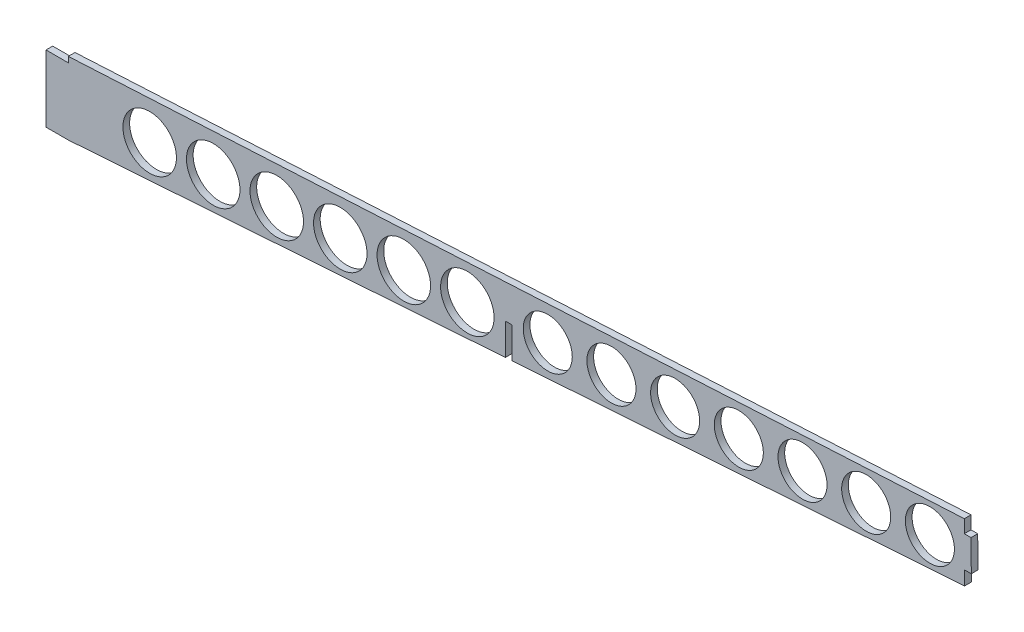
SolidWorks part; units mm, degrees
material "Pine"
ref_plane "Front Plane" through (0, 0, 0) normal (0, 0, 1) x (1, 0, 0)
ref_plane "Top Plane" through (0, 0, 0) normal (0, 1, 0) x (1, 0, 0)
ref_plane "Right Plane" through (0, 0, 0) normal (1, 0, 0) x (0, 0, -1)
sketch "Sketch1" plane through (0, 0, 0) normal (0, 0, 1) x (1, 0, 0)
  line L0 (-415, 15) -> (-405, 15) construction
  line L4 (-415, 0) -> (-415, 30)
  line L6 (-415, 30) -> (-405, 30)
  line L7 (-415, 0) -> (-405, 0)
  line L8 (-415, 0) -> (0, 0) construction
  line L9 (-415, 15) -> (0, 44.0196) construction
  line L10 (-0.2558, 54.0196) -> (0, 28.0209)
  line L11 (0, 44.0196) -> (0, 0) construction
  line L13 (-405, 0) -> (0, 28.0209)
  line L14 (-405, 30) -> (-405, 32.5)
  line L15 (-405, 32.5) -> (-0.2558, 54.0196)
  dimension "D1" = 30
  dimension "D2" = 10
  dimension "D3" = 415
  dimension "D4" = 4
  dimension "D5" = 26
  dimension "D6" = 10
  dimension "D7" = 93.394
  dimension "D8" = 2.5
extrude "Boss-Extrude1" add sketch "Sketch1" along normal blind 3
sketch "Sketch2" plane through (0, 0, 3) normal (0, 0, 1) x (1, 0, 0)
  line L0 (-415, 15.0021) -> (-404.9671, 15.0021) construction
  line L1 (-415, 30) -> (-415, 0) construction
  line L3 (-404.9671, 15.0021) -> (-0.1279, 41.0203) construction
  line L4 (0, 28.0209) -> (-0.2558, 54.0196) construction
  line L5 (-415, 0) -> (0, 0) construction
  line L6 (-207.5, 0) -> (-207.5, 27.6929) construction
  line L7 (-209, 27.6929) -> (-206, 27.6929)
  line L8 (-209, 27.6929) -> (-209, 13.5607)
  line L9 (-405, 0) -> (0, 28.0209) construction
  line L10 (-209, 13.5607) -> (-206, 13.5607)
  line L11 (-206, 13.5607) -> (-206, 27.6929)
  circle A1 centre (-397, 15.5141) radius 12 construction
  circle A2 centre (-368.51, 17.3451) radius 12
  circle A3 centre (-340.0199, 19.1761) radius 12
  circle A4 centre (-311.5299, 21.0071) radius 12
  circle A5 centre (-283.0398, 22.8381) radius 12
  circle A6 centre (-254.5498, 24.6691) radius 12
  circle A11 centre (-190, 28.8176) radius 11
  circle A12 centre (-161.4391, 30.6531) radius 11
  circle A13 centre (-132.8782, 32.4887) radius 11
  circle A14 centre (-104.3174, 34.3242) radius 11
  circle A15 centre (-75.7565, 36.1598) radius 11
  circle A16 centre (-47.1956, 37.9953) radius 11
  circle A17 centre (-18.6347, 39.8309) radius 11
  circle A21 centre (-226.0597, 26.5001) radius 12
  point P4 (0, 0)
  point P6 (-405, 15.5141)
  point P18 (-207.5, 27.6929)
  point P35 (-405, 15.5141)
  point P38 (-405.2691, 15.5141)
  point P39 (-404.6758, 15.5141)
  point P40 (-225.6267, 26.5279)
  point P41 (-283.0398, 22.8381)
  point P42 (-405, 15.5141)
  dimension "D3" = 24
  dimension "D6" = 22
  dimension "D1" = 3
  dimension "D2" = 18
  dimension "D7" = 16
  dimension "D4" = 7
  dimension "D8" = 7
extrude "Cut-Extrude1" cut sketch "Sketch2" against normal through all both and the other way through all
sketch "Sketch3" plane through (0, 0, 3) normal (0, 0, 1) x (1, 0, 0)
  line L10 (-0.2558, 54.0196) -> (-3.1968, 53.8633)
  line L11 (-0.2558, 54.0196) -> (-405, 32.5) construction
  line L12 (-3.1968, 53.8633) -> (-3.1968, 48.0196)
  line L13 (-3.1968, 48.0196) -> (-0.1968, 48.0196)
  line L14 (0, 28.0209) -> (-0.2558, 54.0196) construction
  line L15 (-0.1968, 48.0196) -> (-0.2558, 54.0196)
  line L16 (0, 28.0209) -> (-3.059, 27.8092)
  line L17 (-206, 13.7683) -> (0, 28.0209) construction
  line L18 (-3.059, 27.8092) -> (-3.059, 34.0209)
  line L19 (-3.059, 34.0209) -> (-0.059, 34.0209)
  line L20 (-0.059, 34.0209) -> (0, 28.0209)
  point P14 (-1.6968, 48.0196)
  dimension "D1" = 3
  dimension "D2" = 6
  dimension "D3" = 6
extrude "Cut-Extrude2" cut sketch "Sketch3" against normal blind 10
